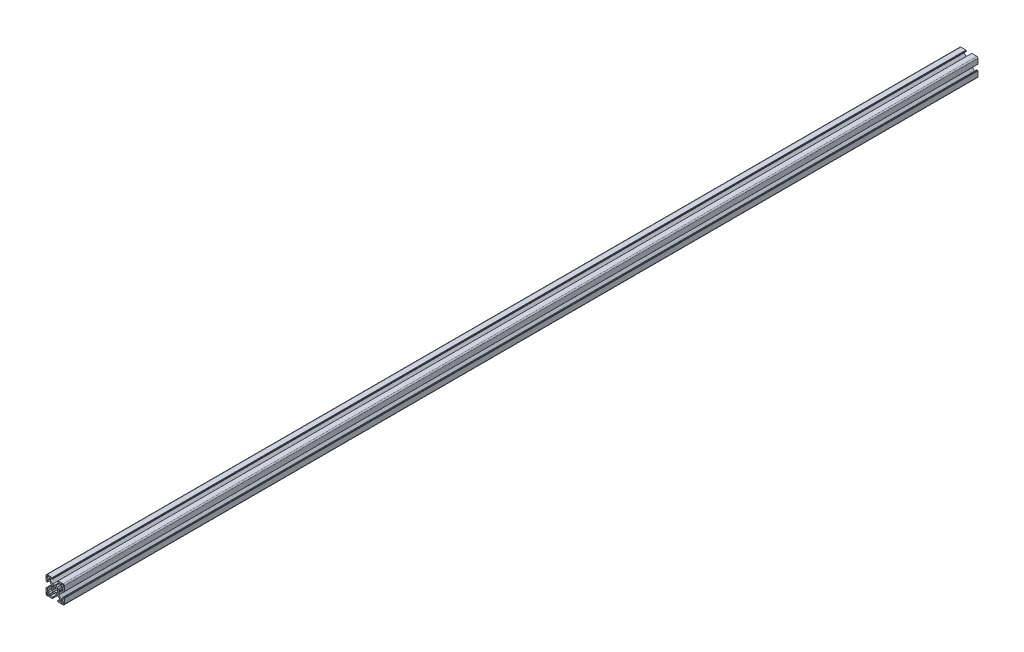
SolidWorks part; units mm, degrees
ref_plane "Płaszczyzna przednia" through (0, 0, 0) normal (0, 0, 1) x (1, 0, 0)
ref_plane "Płaszczyzna górna" through (0, 0, 0) normal (0, 1, 0) x (1, 0, 0)
ref_plane "Płaszczyzna prawa" through (0, 0, 0) normal (1, 0, 0) x (0, 0, -1)
sketch "Sketch1" plane through (0, 0, 0) normal (0, 0, 1) x (1, 0, 0)
  line L0 (109.26, 48.76) -> (107.06, 48.76)
  line L1 (106.06, 47.76) -> (106.06, 45.56)
  line L2 (107.06, 44.56) -> (109.26, 44.56)
  line L3 (110.26, 45.56) -> (110.26, 47.76)
  line L4 (94.9599, 38.3406) -> (93.4241, 39.5784)
  line L5 (92.0547, 38.2147) -> (93.2794, 36.6601)
  line L6 (93.2794, 33.4599) -> (92.0547, 31.9053)
  line L7 (93.4241, 30.5416) -> (94.9599, 31.7794)
  line L8 (98.1601, 31.7794) -> (99.6959, 30.5416)
  line L9 (101.0653, 31.9053) -> (99.8406, 33.4599)
  line L10 (99.8406, 36.6601) -> (101.0653, 38.2147)
  line L11 (99.6959, 39.5784) -> (98.1601, 38.3406)
  line L12 (83.86, 21.36) -> (86.06, 21.36)
  line L13 (87.06, 22.36) -> (87.06, 24.56)
  line L14 (86.06, 25.56) -> (83.86, 25.56)
  line L15 (82.86, 24.56) -> (82.86, 22.36)
  line L16 (110.26, 22.36) -> (110.26, 24.56)
  line L17 (109.26, 25.56) -> (107.06, 25.56)
  line L18 (106.06, 24.56) -> (106.06, 22.36)
  line L19 (86.06, 48.76) -> (83.86, 48.76)
  line L20 (82.86, 47.76) -> (82.86, 45.56)
  line L21 (83.86, 44.56) -> (86.06, 44.56)
  line L22 (87.06, 45.56) -> (87.06, 47.76)
  line L23 (107.06, 21.36) -> (109.26, 21.36)
  line L24 (96.56, 29.5751) -> (97.46, 29.06)
  line L25 (97.46, 29.06) -> (100.7645, 29.06)
  line L26 (100.7645, 29.06) -> (104.81, 25.01)
  line L27 (104.81, 25.01) -> (104.81, 22.46)
  line L28 (104.61, 22.26) -> (101.21, 22.26)
  line L29 (100.61, 21.66) -> (100.61, 20.76)
  line L30 (100.81, 20.56) -> (100.91, 20.56)
  line L31 (101.11, 20.36) -> (101.11, 20.26)
  line L32 (101.31, 20.06) -> (109.56, 20.06)
  line L33 (111.56, 22.06) -> (111.56, 30.31)
  line L34 (111.36, 30.51) -> (111.26, 30.51)
  line L35 (111.06, 30.71) -> (111.06, 30.81)
  line L36 (110.86, 31.01) -> (109.96, 31.01)
  line L37 (109.36, 30.41) -> (109.36, 27.01)
  line L38 (109.16, 26.81) -> (106.61, 26.81)
  line L39 (106.61, 26.81) -> (102.5645, 30.8555)
  line L40 (102.5645, 30.8555) -> (102.5645, 34.16)
  line L41 (102.5645, 34.16) -> (102.0449, 35.06)
  line L42 (102.0449, 35.06) -> (102.5645, 35.96)
  line L43 (102.5645, 35.96) -> (102.5645, 39.2645)
  line L44 (102.5645, 39.2645) -> (106.61, 43.31)
  line L45 (106.61, 43.31) -> (109.16, 43.31)
  line L46 (109.36, 43.11) -> (109.36, 39.71)
  line L47 (109.96, 39.11) -> (110.86, 39.11)
  line L48 (111.06, 39.31) -> (111.06, 39.41)
  line L49 (111.26, 39.61) -> (111.36, 39.61)
  line L50 (111.56, 39.81) -> (111.56, 48.06)
  line L51 (109.56, 50.06) -> (101.31, 50.06)
  line L52 (101.11, 49.86) -> (101.11, 49.76)
  line L53 (100.91, 49.56) -> (100.81, 49.56)
  line L54 (100.61, 49.36) -> (100.61, 48.46)
  line L55 (101.21, 47.86) -> (104.61, 47.86)
  line L56 (104.81, 47.66) -> (104.81, 45.11)
  line L57 (104.81, 45.11) -> (100.7645, 41.06)
  line L58 (100.7645, 41.06) -> (97.46, 41.06)
  line L59 (97.46, 41.06) -> (96.56, 40.5449)
  line L60 (96.56, 40.5449) -> (95.66, 41.06)
  line L61 (95.66, 41.06) -> (92.3555, 41.06)
  line L62 (92.3555, 41.06) -> (88.31, 45.11)
  line L63 (88.31, 45.11) -> (88.31, 47.66)
  line L64 (88.51, 47.86) -> (91.91, 47.86)
  line L65 (92.51, 48.46) -> (92.51, 49.36)
  line L66 (92.31, 49.56) -> (92.21, 49.56)
  line L67 (92.01, 49.76) -> (92.01, 49.86)
  line L68 (91.81, 50.06) -> (83.56, 50.06)
  line L69 (81.56, 48.06) -> (81.56, 39.81)
  line L70 (81.76, 39.61) -> (81.86, 39.61)
  line L71 (82.06, 39.41) -> (82.06, 39.31)
  line L72 (82.26, 39.11) -> (83.16, 39.11)
  line L73 (83.76, 39.71) -> (83.76, 43.11)
  line L74 (83.96, 43.31) -> (86.51, 43.31)
  line L75 (86.51, 43.31) -> (90.5555, 39.2645)
  line L76 (90.5555, 39.2645) -> (90.5555, 35.96)
  line L77 (90.5555, 35.96) -> (91.0751, 35.06)
  line L78 (91.0751, 35.06) -> (90.5555, 34.16)
  line L79 (90.5555, 34.16) -> (90.5555, 30.8555)
  line L80 (90.5555, 30.8555) -> (86.51, 26.81)
  line L81 (86.51, 26.81) -> (83.96, 26.81)
  line L82 (83.76, 27.01) -> (83.76, 30.41)
  line L83 (83.16, 31.01) -> (82.26, 31.01)
  line L84 (82.06, 30.81) -> (82.06, 30.71)
  line L85 (81.86, 30.51) -> (81.76, 30.51)
  line L86 (81.56, 30.31) -> (81.56, 22.06)
  line L87 (83.56, 20.06) -> (91.81, 20.06)
  line L88 (92.01, 20.26) -> (92.01, 20.36)
  line L89 (92.21, 20.56) -> (92.31, 20.56)
  line L90 (92.51, 20.76) -> (92.51, 21.66)
  line L91 (91.91, 22.26) -> (88.51, 22.26)
  line L92 (88.31, 22.46) -> (88.31, 25.01)
  line L93 (88.31, 25.01) -> (92.3555, 29.06)
  line L94 (92.3555, 29.06) -> (95.66, 29.06)
  line L95 (95.66, 29.06) -> (96.56, 29.5751)
  arc A0 (107.06, 48.76) -> (106.06, 47.76) centre (107.06, 47.76) ccw
  arc A1 (106.06, 45.56) -> (107.06, 44.56) centre (107.06, 45.56) ccw
  arc A2 (109.26, 44.56) -> (110.26, 45.56) centre (109.26, 45.56) ccw
  arc A3 (110.26, 47.76) -> (109.26, 48.76) centre (109.26, 47.76) ccw
  arc A4 (93.4241, 39.5784) -> (92.0547, 38.2147) centre (96.56, 35.06) ccw
  arc A5 (93.2794, 36.6601) -> (93.2794, 33.4599) centre (96.56, 35.06) ccw
  arc A6 (92.0547, 31.9053) -> (93.4241, 30.5416) centre (96.56, 35.06) ccw
  arc A7 (94.9599, 31.7794) -> (98.1601, 31.7794) centre (96.56, 35.06) ccw
  arc A8 (99.6959, 30.5416) -> (101.0653, 31.9053) centre (96.56, 35.06) ccw
  arc A9 (99.8406, 33.4599) -> (99.8406, 36.6601) centre (96.56, 35.06) ccw
  arc A10 (101.0653, 38.2147) -> (99.6959, 39.5784) centre (96.56, 35.06) ccw
  arc A11 (98.1601, 38.3406) -> (94.9599, 38.3406) centre (96.56, 35.06) ccw
  arc A12 (86.06, 21.36) -> (87.06, 22.36) centre (86.06, 22.36) ccw
  arc A13 (87.06, 24.56) -> (86.06, 25.56) centre (86.06, 24.56) ccw
  arc A14 (83.86, 25.56) -> (82.86, 24.56) centre (83.86, 24.56) ccw
  arc A15 (82.86, 22.36) -> (83.86, 21.36) centre (83.86, 22.36) ccw
  arc A16 (109.26, 21.36) -> (110.26, 22.36) centre (109.26, 22.36) ccw
  arc A17 (110.26, 24.56) -> (109.26, 25.56) centre (109.26, 24.56) ccw
  arc A18 (107.06, 25.56) -> (106.06, 24.56) centre (107.06, 24.56) ccw
  arc A19 (106.06, 22.36) -> (107.06, 21.36) centre (107.06, 22.36) ccw
  arc A20 (83.86, 48.76) -> (82.86, 47.76) centre (83.86, 47.76) ccw
  arc A21 (82.86, 45.56) -> (83.86, 44.56) centre (83.86, 45.56) ccw
  arc A22 (86.06, 44.56) -> (87.06, 45.56) centre (86.06, 45.56) ccw
  arc A23 (87.06, 47.76) -> (86.06, 48.76) centre (86.06, 47.76) ccw
  arc A24 (104.61, 22.26) -> (104.81, 22.46) centre (104.61, 22.46) ccw
  arc A25 (101.21, 22.26) -> (100.61, 21.66) centre (101.21, 21.66) ccw
  arc A26 (100.61, 20.76) -> (100.81, 20.56) centre (100.81, 20.76) ccw
  arc A27 (101.11, 20.36) -> (100.91, 20.56) centre (100.91, 20.36) ccw
  arc A28 (101.11, 20.26) -> (101.31, 20.06) centre (101.31, 20.26) ccw
  arc A29 (109.56, 20.06) -> (111.56, 22.06) centre (109.56, 22.06) ccw
  arc A30 (111.56, 30.31) -> (111.36, 30.51) centre (111.36, 30.31) ccw
  arc A31 (111.06, 30.71) -> (111.26, 30.51) centre (111.26, 30.71) ccw
  arc A32 (111.06, 30.81) -> (110.86, 31.01) centre (110.86, 30.81) ccw
  arc A33 (109.96, 31.01) -> (109.36, 30.41) centre (109.96, 30.41) ccw
  arc A34 (109.16, 26.81) -> (109.36, 27.01) centre (109.16, 27.01) ccw
  arc A35 (109.36, 43.11) -> (109.16, 43.31) centre (109.16, 43.11) ccw
  arc A36 (109.36, 39.71) -> (109.96, 39.11) centre (109.96, 39.71) ccw
  arc A37 (110.86, 39.11) -> (111.06, 39.31) centre (110.86, 39.31) ccw
  arc A38 (111.26, 39.61) -> (111.06, 39.41) centre (111.26, 39.41) ccw
  arc A39 (111.36, 39.61) -> (111.56, 39.81) centre (111.36, 39.81) ccw
  arc A40 (111.56, 48.06) -> (109.56, 50.06) centre (109.56, 48.06) ccw
  arc A41 (101.31, 50.06) -> (101.11, 49.86) centre (101.31, 49.86) ccw
  arc A42 (100.91, 49.56) -> (101.11, 49.76) centre (100.91, 49.76) ccw
  arc A43 (100.81, 49.56) -> (100.61, 49.36) centre (100.81, 49.36) ccw
  arc A44 (100.61, 48.46) -> (101.21, 47.86) centre (101.21, 48.46) ccw
  arc A45 (104.81, 47.66) -> (104.61, 47.86) centre (104.61, 47.66) ccw
  arc A46 (88.51, 47.86) -> (88.31, 47.66) centre (88.51, 47.66) ccw
  arc A47 (91.91, 47.86) -> (92.51, 48.46) centre (91.91, 48.46) ccw
  arc A48 (92.51, 49.36) -> (92.31, 49.56) centre (92.31, 49.36) ccw
  arc A49 (92.01, 49.76) -> (92.21, 49.56) centre (92.21, 49.76) ccw
  arc A50 (92.01, 49.86) -> (91.81, 50.06) centre (91.81, 49.86) ccw
  arc A51 (83.56, 50.06) -> (81.56, 48.06) centre (83.56, 48.06) ccw
  arc A52 (81.56, 39.81) -> (81.76, 39.61) centre (81.76, 39.81) ccw
  arc A53 (82.06, 39.41) -> (81.86, 39.61) centre (81.86, 39.41) ccw
  arc A54 (82.06, 39.31) -> (82.26, 39.11) centre (82.26, 39.31) ccw
  arc A55 (83.16, 39.11) -> (83.76, 39.71) centre (83.16, 39.71) ccw
  arc A56 (83.96, 43.31) -> (83.76, 43.11) centre (83.96, 43.11) ccw
  arc A57 (83.76, 27.01) -> (83.96, 26.81) centre (83.96, 27.01) ccw
  arc A58 (83.76, 30.41) -> (83.16, 31.01) centre (83.16, 30.41) ccw
  arc A59 (82.26, 31.01) -> (82.06, 30.81) centre (82.26, 30.81) ccw
  arc A60 (81.86, 30.51) -> (82.06, 30.71) centre (81.86, 30.71) ccw
  arc A61 (81.76, 30.51) -> (81.56, 30.31) centre (81.76, 30.31) ccw
  arc A62 (81.56, 22.06) -> (83.56, 20.06) centre (83.56, 22.06) ccw
  arc A63 (91.81, 20.06) -> (92.01, 20.26) centre (91.81, 20.26) ccw
  arc A64 (92.21, 20.56) -> (92.01, 20.36) centre (92.21, 20.36) ccw
  arc A65 (92.31, 20.56) -> (92.51, 20.76) centre (92.31, 20.76) ccw
  arc A66 (92.51, 21.66) -> (91.91, 22.26) centre (91.91, 21.66) ccw
  arc A67 (88.31, 22.46) -> (88.51, 22.26) centre (88.51, 22.46) ccw
  dimension "D1" = 3.65
  dimension "D2" = 30
  dimension "D3" = 30
  dimension "D4" = 8.1
extrude "Sigma Profile" add sketch "Sketch1" along normal blind 1500
